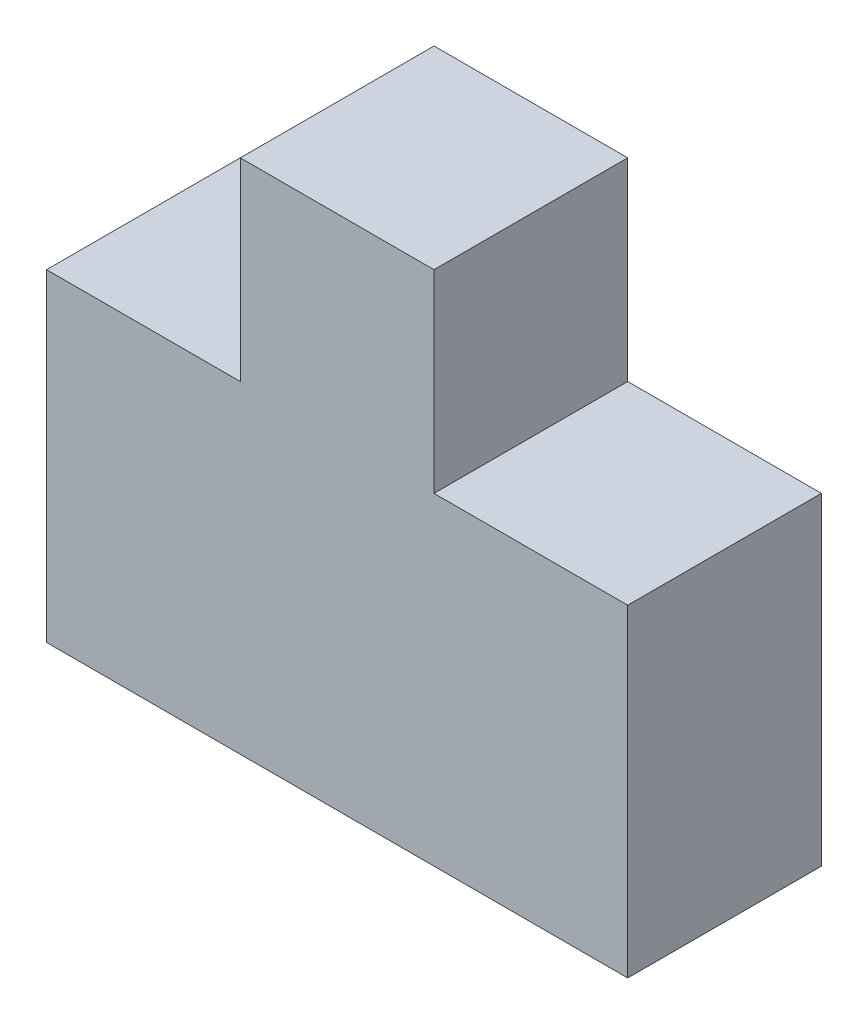
SolidWorks part; units mm, degrees
ref_plane "Front Plane" through (0, 0, 0) normal (0, 0, 1) x (1, 0, 0)
ref_plane "Top Plane" through (0, 0, 0) normal (0, 1, 0) x (1, 0, 0)
ref_plane "Right Plane" through (0, 0, 0) normal (1, 0, 0) x (0, 0, -1)
sketch "Sketch2" plane through (0, 0, 0) normal (0, 0, 1) x (1, 0, 0)
  line L0 (-45, 0) -> (45, 0)
  line L1 (45, 0) -> (45, 50)
  line L2 (45, 50) -> (15, 50)
  line L3 (-15, 50) -> (-15, 80)
  line L4 (-15, 80) -> (15, 80)
  line L5 (0, 20) -> (0, -19.7074) construction
  line L6 (15, 80) -> (15, 50)
  line L7 (-45, 50) -> (-15, 50)
  line L8 (-45, 0) -> (-45, 50)
  point P12 (0, 0)
  dimension "D1" = 50
  dimension "D2" = 90
  dimension "D3" = 30
  dimension "D4" = 30
extrude "Boss-Extrude1" add sketch "Sketch2" along normal blind 30
